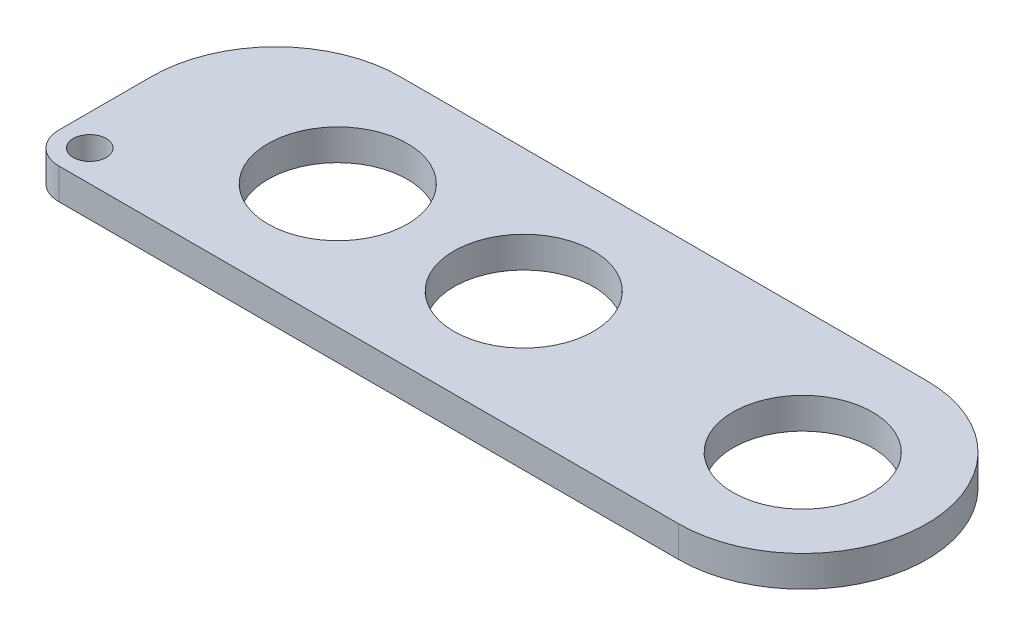
SolidWorks part; units mm, degrees
ref_plane "Front" through (0, 0, 0) normal (0, 0, 1) x (1, 0, 0)
ref_plane "Top" through (0, 0, 0) normal (0, 1, 0) x (1, 0, 0)
ref_plane "Right" through (0, 0, 0) normal (1, 0, 0) x (0, 0, -1)
sketch "Sketch3" plane through (0, 0, 0) normal (0, 1, 0) x (1, 0, 0)
  point P0 (0, 0)
  point P1 (38.1, 0)
  point P3 (95.25, 0)
  point P4 (0, 0)
  point P5 (0, 0)
  point P6 (0, 0)
  dimension "D1" = 38.1
  dimension "D2" = 57.15
sketch "Sketch1" plane through (0, 0, 0) normal (0, 1, 0) x (1, 0, 0)
  line L0 (-38.1, 25.4) -> (95.25, 25.4)
  line L5 (95.25, -25.4) -> (-38.1, -25.4)
  line L6 (-38.1, 25.4) -> (-38.1, -25.4)
  arc A2 (95.25, -25.4) -> (95.25, 25.4) centre (95.25, 0) ccw
  dimension "D1" = 38.1
  dimension "D2" = 25.4
extrude "Boss-Extrude1" add sketch "Sketch1" along normal blind 6.35
sketch "Sketch2" plane through (0, 6.35, 0) normal (0, 1, 0) x (1, 0, 0)
  circle A0 centre (38.1, 0) radius 14.2875
  circle A1 centre (95.25, 0) radius 14.2875
  circle A2 centre (0, 0) radius 14.2875
  point P8 (0, 0)
  point P10 (0, 0)
  point P12 (0, 0)
  point P13 (0, 0)
  point P14 (0, 0)
  point P15 (0, 0)
  point P16 (1.9009, -5.0012)
  point P18 (0, 0)
  dimension "D1" = 28.575
  dimension "D2" = 38.1
  dimension "D3" = 57.15
extrude "Cut-Extrude1" cut sketch "Sketch2" along direction (0, 1, 0) on the side against the normal through all contours A2 | A0 | A1
hole_wizard "1/4 Clearance Hole1" positions "Sketch4" profile "Sketch5" hole size "1/4" standard "ANSI Inch" end condition through all
sketch "Sketch4" plane through (0, 6.35, 0) normal (0, 1, 0) x (1, 0, 0)
  point P0 (-31.75, -19.05)
  point P6 (-31.75, -17.4423)
  dimension "D1" = 31.75
  dimension "D2" = 19.05
sketch "Sketch5" plane through (-31.75, 6.35, 19.05) normal (1, 0, 0) x (0, 0, 1)
  line L0 (0, 0) -> (0, 6.35)
  line L1 (0, 6.35) -> (3.3782, 6.35)
  line L2 (3.3782, 6.35) -> (3.3782, 0)
  line L5 (3.3782, 0) -> (0, 0)
  line L11 (0, -6.35) -> (0, 107.95) construction
  dimension "Thru Hole Dia." = 6.7564
  dimension "Thru Hole Depth" = 6.35
fillet "Fillet1" radius 6.35 1 edges at (-38.1, 3.175, 25.4)
fillet "Fillet2" radius 25.4 1 edges at (-38.1, 3.175, -25.4)
